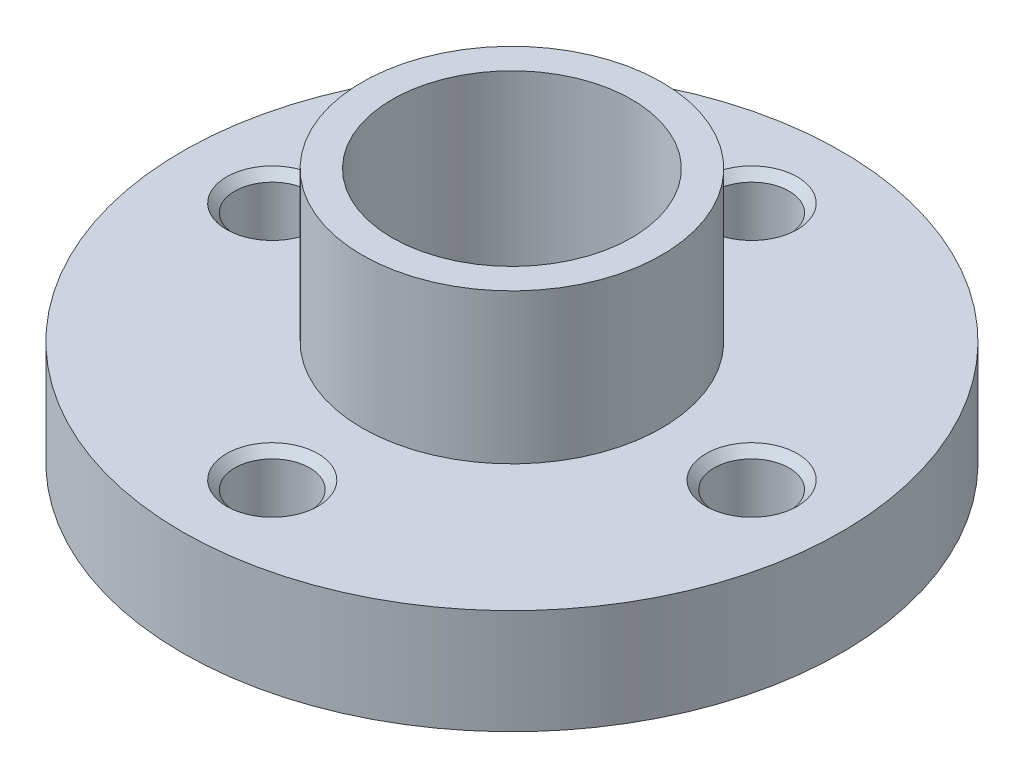
SolidWorks part; units mm, degrees
material "黄铜"
ref_plane "前视基准面" through (0, 0, 0) normal (0, 0, 1) x (1, 0, 0)
ref_plane "上视基准面" through (0, 0, 0) normal (0, 1, 0) x (1, 0, 0)
ref_plane "右视基准面" through (0, 0, 0) normal (1, 0, 0) x (0, 0, -1)
sketch "草图1" plane through (0, 0, 0) normal (0, 1, 0) x (1, 0, 0)
  circle A0 centre (0, 0) radius 11
  dimension "D1" = 22
extrude "凸台-拉伸1" add sketch "草图1" along normal blind 3.5
sketch "草图2" plane through (0, 3.5, 0) normal (0, 1, 0) x (1, 0, 0)
  circle A0 centre (0, 0) radius 5
  dimension "D1" = 10
extrude "凸台-拉伸2" add sketch "草图2" along normal blind 5 and the other way blind 5.5
sketch "草图3" plane through (0, 3.5, 0) normal (0, 1, 0) x (1, 0, 0)
  circle A0 centre (0, 0) radius 8 construction
  circle A1 centre (0, 8) radius 1.15
  circle A2 centre (8, 0) radius 1.15
  circle A3 centre (0, -8) radius 1.15
  circle A4 centre (-8, 0) radius 1.15
  point P14 (0, 0)
  dimension "D1" = 16
  dimension "D2" = 2.3
  dimension "D3" = 4
extrude "切除-拉伸1" cut sketch "草图3" against normal blind 5
sketch "草图4" plane through (0, 8.5, 0) normal (0, 1, 0) x (1, 0, 0)
  circle A0 centre (0, 0) radius 4
  dimension "D1" = 8
extrude "切除-拉伸2" cut sketch "草图4" against normal through all
hole_wizard "M3 螺纹孔1" positions "草图5" profile "草图6" tap size "M3" standard "GB"
sketch "草图5" plane through (0, 3.5, 0) normal (0, 1, 0) x (1, 0, 0)
  point P0 (0, 8)
  point P3 (8, 0)
  point P6 (0, -8)
  point P9 (-8, 0)
sketch "草图6" plane through (0, 3.5, -8) normal (1, 0, 0) x (0, 0, 1)
  line L0 (0, 0) -> (0, 9.2511)
  line L1 (0, 9.2511) -> (1.25, 8.5)
  line L2 (1.25, 8.5) -> (1.25, 0.275)
  line L3 (1.25, 0.275) -> (1.525, 0)
  line L5 (1.525, 0) -> (0, 0)
  line L6 (-1.25, 0.275) -> (-1.525, 0) construction
  line L10 (0, 9.2511) -> (-1.25, 8.5) construction
  line L11 (0, -6.35) -> (0, 107.95) construction
  dimension "螺纹孔钻头直径" = 2.5
  dimension "螺纹孔钻头深度" = 8.5
  dimension "近端锥形沉头孔直径" = 3.05
  dimension "近端锥形沉头孔角度" = 90
  dimension "导头角度" = 118
cosmetic thread "孔螺蚊线1" parameters "D1"=6, "D2"=3
cosmetic thread "孔螺蚊线2" parameters "D1"=6, "D2"=3
cosmetic thread "孔螺蚊线3" parameters "D1"=6, "D2"=3
cosmetic thread "孔螺蚊线4" parameters "D1"=6, "D2"=3
